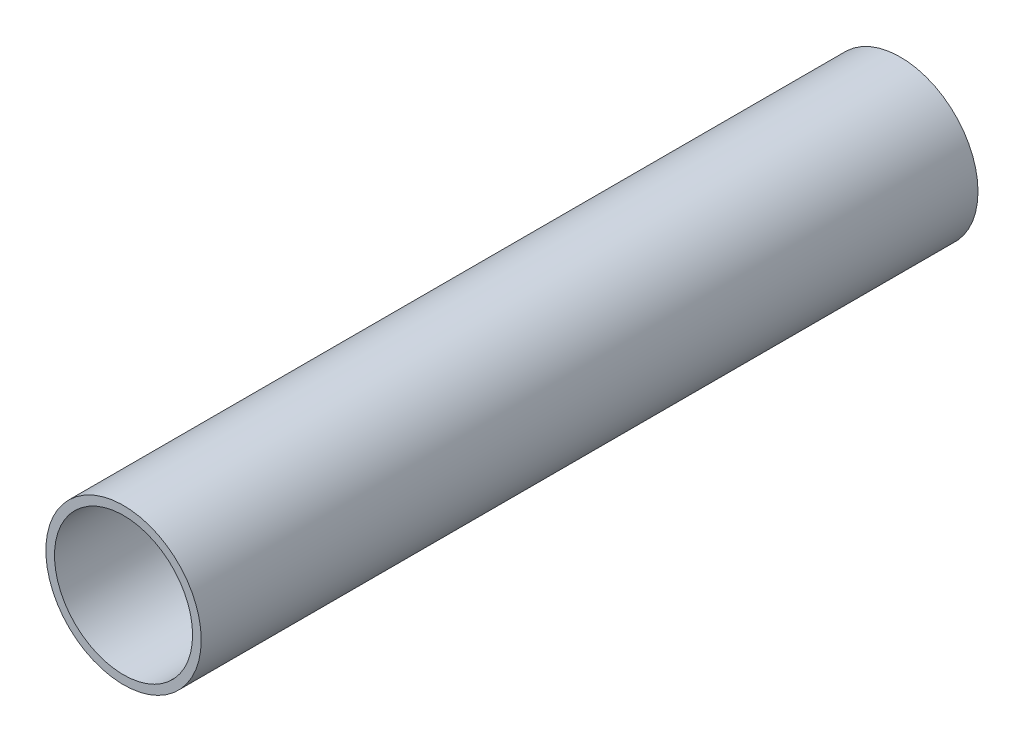
SolidWorks part; units mm, degrees
ref_plane "Front Plane" through (0, 0, 0) normal (0, 0, 1) x (1, 0, 0)
ref_plane "Top Plane" through (0, 0, 0) normal (0, 1, 0) x (1, 0, 0)
ref_plane "Right Plane" through (0, 0, 0) normal (1, 0, 0) x (0, 0, -1)
sketch "Sketch1" plane through (0, 0, 0) normal (0, 0, 1) x (1, 0, 0)
  circle A0 centre (0, 0) radius 16
  circle A1 centre (0, 0) radius 18
  dimension "D1" = 36
  dimension "D2" = 32
extrude "Boss-Extrude1" add sketch "Sketch1" along normal blind 180
